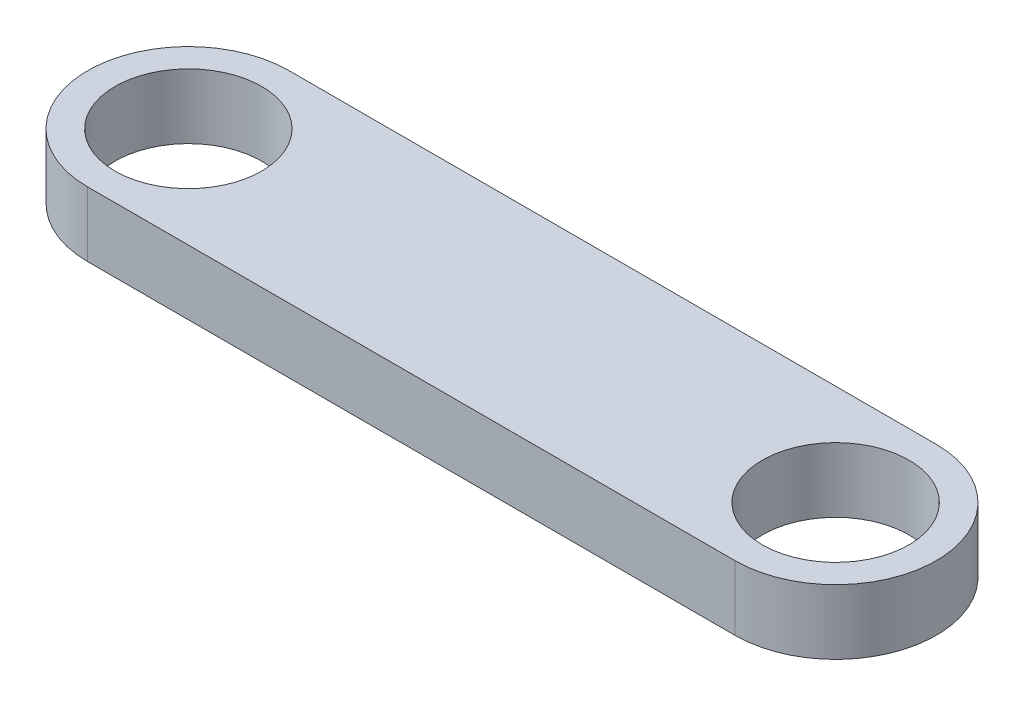
SolidWorks part; units mm, degrees
ref_plane "Front Plane" through (0, 0, 0) normal (0, 0, 1) x (1, 0, 0)
ref_plane "Top Plane" through (0, 0, 0) normal (0, 1, 0) x (1, 0, 0)
ref_plane "Right Plane" through (0, 0, 0) normal (1, 0, 0) x (0, 0, -1)
other "Center of Mass"
sketch "Sketch1" plane through (0, 0, 0) normal (0, 1, 0) x (1, 0, 0)
  line L1 (-22.5, -7) -> (22.5, -7)
  line L2 (-22.5, -7) -> (-22.5, 7)
  line L3 (-22.5, 7) -> (22.5, 7)
  line L4 (22.5, -7) -> (22.5, 7)
  line L5 (-22.5, -7) -> (22.5, 7) construction
  line L6 (-22.5, 7) -> (22.5, -7) construction
  circle A0 centre (-22.5, 0) radius 7
  circle A1 centre (22.5, 0) radius 7
  circle A2 centre (-22.5, 0) radius 5.1
  circle A3 centre (22.5, 0) radius 5.1
  point P0 (0, 0)
  dimension "D2" = 10.2
  dimension "D1" = 45
  dimension "D4" = 14
extrude "Boss-Extrude1" add sketch "Sketch1" along normal blind 4.5 contours A2 L2 A0 | A2 L2 A0 | A1 L3 A0 L1 | A3 L4 A1 | A3 L4 A1
sketch "Sketch2" plane through (0, 4.5, 0) normal (0, 1, 0) x (1, 0, 0)
  line L0 (0, 0) -> (0, -44.132) construction
  line L3 (22.5, 7) -> (-22.5, 7)
  line L4 (-22.5, -7) -> (22.5, -7)
  line L5 (22.5, 7) -> (-22.5, 7)
  line L6 (-22.5, -7) -> (22.5, -7)
  arc A0 (-22.5, 7) -> (-22.5, -7) centre (-22.5, 0) ccw construction
  arc A1 (22.5, -7) -> (22.5, 7) centre (22.5, 0) ccw construction
  arc A4 (22.5, -7) -> (22.5, 7) centre (22.5, 0) ccw
  arc A5 (-22.5, 7) -> (-22.5, -7) centre (-22.5, 0) ccw
  arc A6 (22.5, -7) -> (22.5, 7) centre (22.5, 0) ccw
  arc A7 (-22.5, 7) -> (-22.5, -7) centre (-22.5, 0) ccw
  spline S0 degree 2 poles (-29.5, 0) (8.5852, -44.0664) (66.8617, -15.2355) knots 0 0 0 1 1 1
  spline S1 degree 2 poles (29.5, 0) (26.4779, -64.0047) (-15.3333, -51.3437) knots 0 0 0 1 1 1
  line M8 (-22.5, -7) -> (22.5, -7)
  dimension "D1" = 0
extrude "Boss-Extrude2" [suppressed] add sketch "Sketch2" against normal up to surface (4.5 mm away) contours L0 L6 S0 S1 | L0 S1 M8
sketch "Sketch3" plane through (0, 4.5, 0) normal (0, 1, 0) x (1, 0, 0)
  line L0 (0, 0) -> (23.0278, 0) construction
  circle A0 centre (20.5835, 0) radius 2.5
  circle A1 centre (10.5835, 0) radius 2.5
  circle A2 centre (0.5835, 0) radius 2.5
  circle A3 centre (-9.4165, 0) radius 2.5
  circle A4 centre (-19.4165, 0) radius 2.5
  dimension "D1" = 5
  dimension "D2" = 5
extrude "Cut-Extrude1" [suppressed] cut sketch "Sketch3" against normal blind 10
fillet "Fillet1" [suppressed] radius 10
